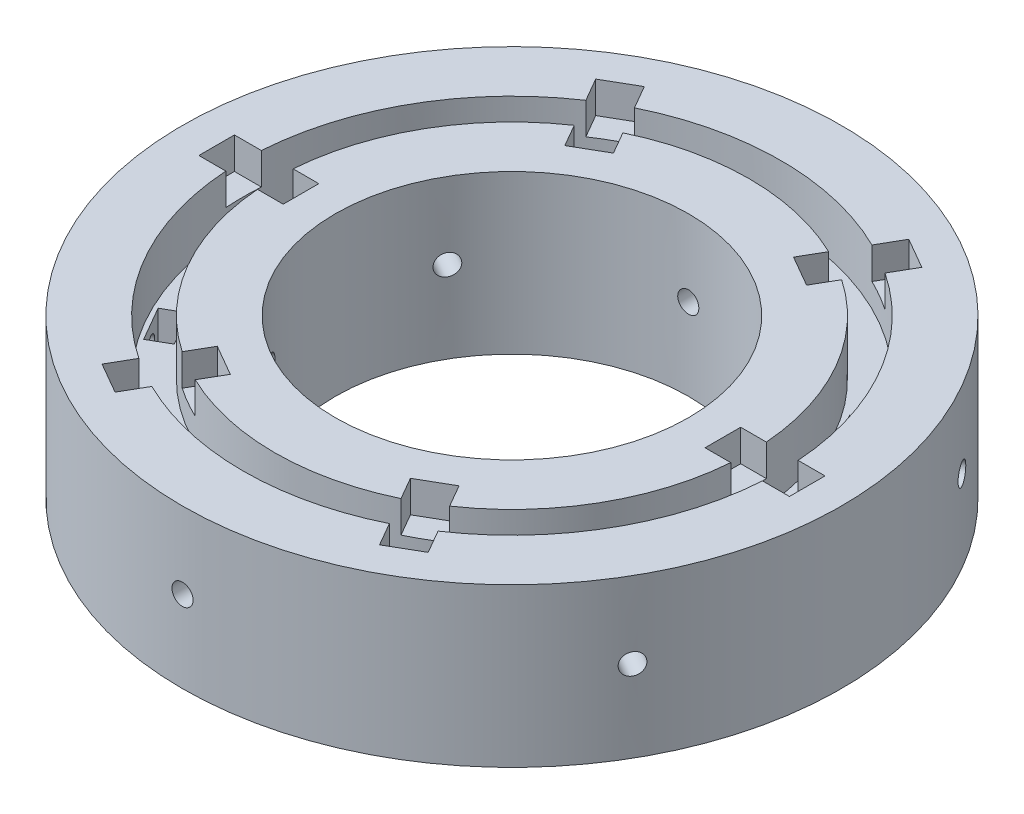
SolidWorks part; units mm, degrees
ref_plane "Front Plane" through (0, 0, 0) normal (0, 0, 1) x (1, 0, 0)
ref_plane "Top Plane" through (0, 0, 0) normal (0, 1, 0) x (1, 0, 0)
ref_plane "Right Plane" through (0, 0, 0) normal (1, 0, 0) x (0, 0, -1)
sketch "Sketch1" plane through (0, 0, 0) normal (0, 1, 0) x (1, 0, 0)
  circle A0 centre (0, 0) radius 62.5
  circle A1 centre (0, 0) radius 33.5
  dimension "D1" = 125
  dimension "D2" = 67
extrude "Boss-Extrude1" add sketch "Sketch1" along normal blind 30 contours A0
sketch "Sketch2" plane through (0, 30, 0) normal (0, 1, 0) x (1, 0, 0)
  line L0 (33.5, 0) -> (62.5, 0) construction
  line L1 (48, 0) -> (48, 3.4672) construction
  line L2 (40, 3.375) -> (56, 3.375)
  line L3 (40, 3.375) -> (40, -3.375)
  line L4 (40, -3.375) -> (56, -3.375)
  line L5 (56, 3.375) -> (56, -3.375)
  line L6 (22.9228, -32.9535) -> (17.0772, -36.3285)
  line L7 (22.9228, -32.9535) -> (30.9228, -46.8099)
  line L8 (30.9228, -46.8099) -> (25.0772, -50.1849)
  line L9 (17.0772, -36.3285) -> (25.0772, -50.1849)
  line L10 (-17.0772, -36.3285) -> (-22.9228, -32.9535)
  line L11 (-17.0772, -36.3285) -> (-25.0772, -50.1849)
  line L12 (-25.0772, -50.1849) -> (-30.9228, -46.8099)
  line L13 (-22.9228, -32.9535) -> (-30.9228, -46.8099)
  line L14 (-40, -3.375) -> (-40, 3.375)
  line L15 (-40, -3.375) -> (-56, -3.375)
  line L16 (-56, -3.375) -> (-56, 3.375)
  line L17 (-40, 3.375) -> (-56, 3.375)
  line L18 (-22.9228, 32.9535) -> (-17.0772, 36.3285)
  line L19 (-22.9228, 32.9535) -> (-30.9228, 46.8099)
  line L20 (-30.9228, 46.8099) -> (-25.0772, 50.1849)
  line L21 (-17.0772, 36.3285) -> (-25.0772, 50.1849)
  line L22 (17.0772, 36.3285) -> (22.9228, 32.9535)
  line L23 (17.0772, 36.3285) -> (25.0772, 50.1849)
  line L24 (25.0772, 50.1849) -> (30.9228, 46.8099)
  line L25 (22.9228, 32.9535) -> (30.9228, 46.8099)
  circle A0 centre (0, 0) radius 48 construction
  circle A1 centre (0, 0) radius 33.5 construction
  circle A2 centre (0, 0) radius 62.5 construction
  point P10 (48, 0)
  point P17 (48, 3.375)
  point P18 (56, 0)
  point P41 (0, 0)
  dimension "D1" = 16
  dimension "D2" = 6.75
  dimension "D3" = 6
extrude "Cut-Extrude2" cut sketch "Sketch2" against normal blind 6
sketch "Sketch3" plane through (0, 30, 0) normal (0, 1, 0) x (1, 0, 0)
  line L0 (33.5, 0) -> (62.5, 0) construction
  line L1 (33.5, 0) -> (62.5, 0) construction
  line L3 (45.625, 7.25) -> (50.375, 7.25) construction
  line L4 (45.625, 7.25) -> (45.625, -7.25) construction
  line L5 (45.625, -7.25) -> (50.375, -7.25) construction
  line L6 (50.375, 7.25) -> (50.375, -7.25) construction
  circle A0 centre (0, 0) radius 48 construction
  circle A1 centre (0, 0) radius 48 construction
  circle A2 centre (0, 0) radius 51
  circle A3 centre (0, 0) radius 45
  point P9 (50.375, 0)
  point P10 (48, 7.25)
  dimension "D1" = 14.5
  dimension "D2" = 4.75
  dimension "D3" = 3
  dimension "D4" = 3
extrude "Cut-Extrude3" cut sketch "Sketch3" against normal blind 10.5 contours A2 | A3
ref_plane "Plane1" through (-19.5138, 30, 40.5489) normal (0.9011, 0, 0.4336) x (0.4336, 0, -0.9011)
sketch "Sketch6" plane through (0, 19.5, 0) normal (0, 1, 0) x (1, 0, 0)
  line L0 (0, 50.125) -> (0, 51) construction
  line L1 (-3.75, 50.125) -> (3.75, 50.125)
  line L2 (-3.75, 50.125) -> (-3.75, 45.875)
  line L3 (-3.75, 45.875) -> (3.75, 45.875)
  line L4 (3.75, 50.125) -> (3.75, 45.875)
  line L5 (-3.75, 50.125) -> (3.75, 45.875) construction
  line L6 (-3.75, 45.875) -> (3.75, 50.125) construction
  line L7 (0, 45.875) -> (0, 45) construction
  line L8 (41.5345, 28.3101) -> (37.8539, 26.1851)
  line L9 (41.5345, 28.3101) -> (45.2845, 21.8149)
  line L10 (45.2845, 21.8149) -> (41.6039, 19.6899)
  line L11 (37.8539, 26.1851) -> (41.6039, 19.6899)
  line L12 (45.2845, -21.8149) -> (41.6039, -19.6899)
  line L13 (45.2845, -21.8149) -> (41.5345, -28.3101)
  line L14 (41.5345, -28.3101) -> (37.8539, -26.1851)
  line L15 (41.6039, -19.6899) -> (37.8539, -26.1851)
  line L16 (3.75, -50.125) -> (3.75, -45.875)
  line L17 (3.75, -50.125) -> (-3.75, -50.125)
  line L18 (-3.75, -50.125) -> (-3.75, -45.875)
  line L19 (3.75, -45.875) -> (-3.75, -45.875)
  line L20 (-41.5345, -28.3101) -> (-37.8539, -26.1851)
  line L21 (-41.5345, -28.3101) -> (-45.2845, -21.8149)
  line L22 (-45.2845, -21.8149) -> (-41.6039, -19.6899)
  line L23 (-37.8539, -26.1851) -> (-41.6039, -19.6899)
  line L24 (-45.2845, 21.8149) -> (-41.6039, 19.6899)
  line L25 (-45.2845, 21.8149) -> (-41.5345, 28.3101)
  line L26 (-41.5345, 28.3101) -> (-37.8539, 26.1851)
  line L27 (-41.6039, 19.6899) -> (-37.8539, 26.1851)
  circle A0 centre (0, 0) radius 51 construction
  arc A1 (19.5138, 40.5489) -> (-19.5138, 40.5489) centre (0, 0) ccw construction
  point P0 (0, 48)
  point P38 (0, 0)
  dimension "D1" = 7.5
  dimension "D2" = 4.25
  dimension "D3" = 6
extrude "Cut-Extrude4" cut sketch "Sketch6" against normal blind 8
sketch "Sketch8" plane through (0, 0, -50.125) normal (0, 0, 1) x (1, 0, 0)
  line L0 (0, 15.5) -> (0, 19.5) construction
  line L1 (3.75, 19.5) -> (-3.75, 19.5) construction
  line L2 (0, 15.5) -> (0, 11.5) construction
  line L4 (3.75, 11.5) -> (-3.75, 11.5) construction
  circle A0 centre (0, 15.5) radius 2
  dimension "D1" = 4
extrude "Cut-Extrude5" cut sketch "Sketch8" along direction (0, 0, -1) on the side against the normal up to surface and the other way up to surface (46.75 mm away)
pattern_circular "CirPattern1" count 6 over 360 about axis through (0, 19.5, 0) along (0, 1, 0) of "Cut-Extrude5"
